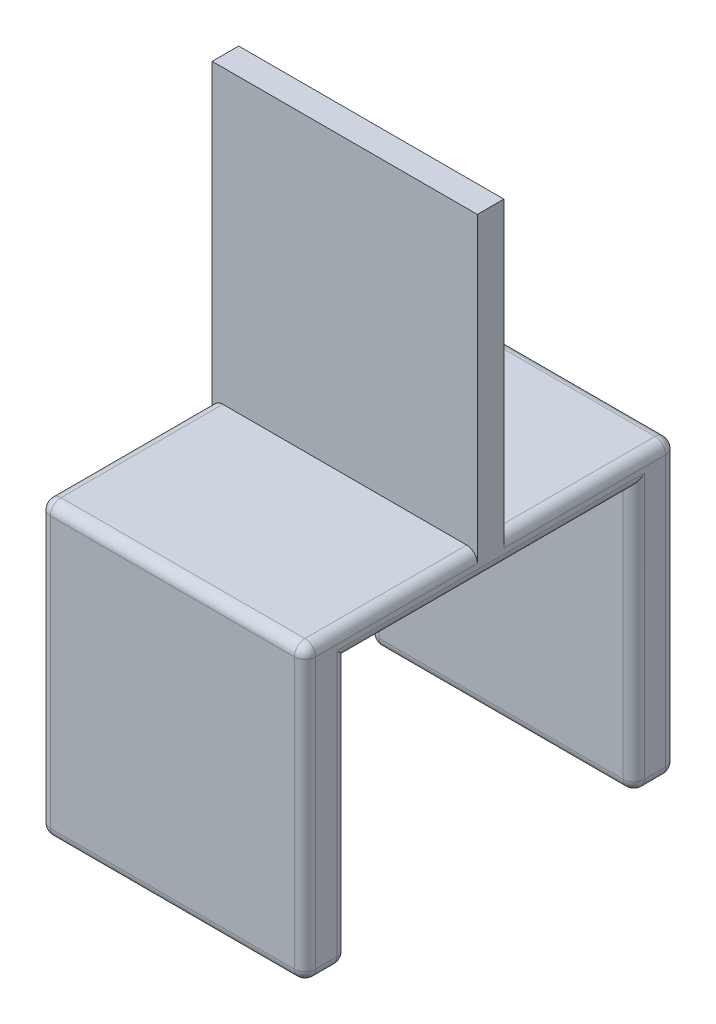
SolidWorks part; units mm, degrees
ref_plane "Front" through (0, 0, 0) normal (0, 0, 1) x (1, 0, 0)
ref_plane "Top" through (0, 0, 0) normal (0, 1, 0) x (1, 0, 0)
ref_plane "Right" through (0, 0, 0) normal (1, 0, 0) x (0, 0, -1)
sketch "Sketch1" plane through (0, 0, 0) normal (0, 0, 1) x (1, 0, 0)
  line L0 (-61.599, 5) -> (22.5954, 5) construction
  line L1 (0, 0) -> (-50, 0)
  line L2 (0, 0) -> (0, 55)
  line L3 (0, 55) -> (-50, 55)
  line L4 (-50, 0) -> (-50, 55)
  dimension "D1" = 50
  dimension "D2" = 55
  dimension "D3" = 5
extrude "Boss-Extrude1" add sketch "Sketch1" along normal blind 5
sketch "Sketch2" plane through (0, 0, 0) normal (0, 1, 0) x (1, 0, 0)
  line L0 (-50, -5) -> (0, -5) construction
  line L1 (-50, 32.5) -> (0, 32.5)
  line L2 (-50, 32.5) -> (-50, -37.5)
  line L3 (-50, -37.5) -> (0, -37.5)
  line L4 (0, 32.5) -> (0, -37.5)
  point P4 (-50, -2.5)
  dimension "D1" = 70
  dimension "D2" = 50
  dimension "D3" = 2.5
  dimension "D4" = 35
extrude "Boss-Extrude2" add sketch "Sketch2" against normal blind 5
ref_plane "Plane1" through (0, -5, 0) normal (0, -1, 0) x (-1, 0, 0)
sketch "Sketch3" plane through (0, -5, 0) normal (0, -1, 0) x (-1, 0, 0)
  line L0 (0, -37.5) -> (0, 32.5) construction
  line L1 (50, -37.5) -> (0, -37.5)
  line L2 (50, -37.5) -> (50, -29.5)
  line L3 (50, -29.5) -> (0, -29.5)
  line L4 (0, -37.5) -> (0, -29.5)
  line L6 (50, 32.5) -> (0, 32.5)
  line L7 (50, 32.5) -> (50, 24.5)
  line L8 (50, 24.5) -> (0, 24.5)
  line L9 (0, 32.5) -> (0, 24.5)
  dimension "D1" = 8
  dimension "D2" = 8
extrude "Boss-Extrude3" add sketch "Sketch3" along normal blind 50 contours L2 L1 L4 L3 | L7 L6 L9 L8
fillet "Fillet1" radius 2 24 edges at (-25, 0, 37.5) (-50, -5, 2.5) (-50, 0, 21.25) (-50, 0, -16.25) (-25, -55, 29.5) (-25, -55, 37.5) (-50, -55, 33.5) (-25, -55, -24.5) (-25, -55, -32.5) (-50, -55, -28.5) (0, -55, -28.5) (0, -55, 33.5) (0, 0, -16.25) (0, 0, 21.25) (0, -5, 2.5) (-25, 0, -32.5) (0, -27.5, -32.5) (-50, -27.5, -32.5) (-50, -30, -24.5) (0, -30, -24.5) (-50, -30, 29.5) (-50, -27.5, 37.5) (0, -27.5, 37.5) (0, -30, 29.5)
